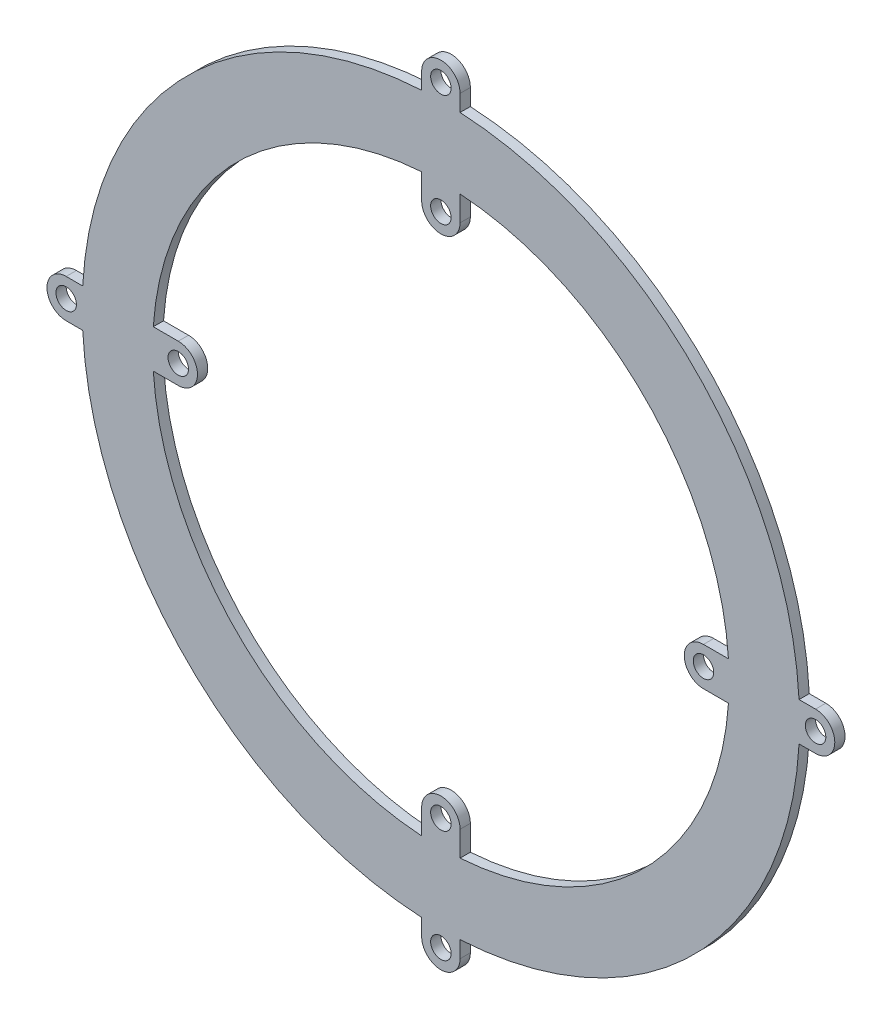
SolidWorks part; units mm, degrees
ref_plane "Front" through (0, 0, 0) normal (0, 0, 1) x (1, 0, 0)
ref_plane "Top" through (0, 0, 0) normal (0, 1, 0) x (1, 0, 0)
ref_plane "Right" through (0, 0, 0) normal (1, 0, 0) x (0, 0, -1)
sketch "Sketch1" plane through (0, 0, 0) normal (0, 0, 1) x (1, 0, 0)
  line L0 (58.5, 3) -> (55.9196, 3)
  line L1 (-3, 58.5) -> (-3, 55.9196)
  line L2 (3, 58.5) -> (3, 55.9196)
  line L3 (58.5, -3) -> (55.9196, -3)
  line L4 (3, -58.5) -> (3, -55.9196)
  line L5 (-3, -58.5) -> (-3, -55.9196)
  line L6 (-58.5, -3) -> (-55.9196, -3)
  line L7 (-58.5, 3) -> (-55.9196, 3)
  line L8 (41, 3) -> (44.8999, 3)
  line L9 (-3, 41) -> (-3, 44.8999)
  line L10 (3, 41) -> (3, 44.8999)
  line L11 (41, -3) -> (44.8999, -3)
  line L12 (3, -41) -> (3, -44.8999)
  line L13 (-3, -41) -> (-3, -44.8999)
  line L14 (-41, -3) -> (-44.8999, -3)
  line L15 (-41, 3) -> (-44.8999, 3)
  arc A0 (-3, 55.9196) -> (-55.9196, 3) centre (0, 0) ccw
  arc A1 (3, 58.5) -> (-3, 58.5) centre (0, 58.5) ccw
  circle A3 centre (0, 58.5) radius 1.6
  arc A4 (58.5, -3) -> (58.5, 3) centre (58.5, 0) ccw
  arc A5 (55.9196, 3) -> (3, 55.9196) centre (0, 0) ccw
  circle A6 centre (58.5, 0) radius 1.6
  arc A7 (-3, -58.5) -> (3, -58.5) centre (0, -58.5) ccw
  arc A8 (3, -55.9196) -> (55.9196, -3) centre (0, 0) ccw
  circle A9 centre (0, -58.5) radius 1.6
  arc A10 (-58.5, 3) -> (-58.5, -3) centre (-58.5, 0) ccw
  arc A11 (-55.9196, -3) -> (-3, -55.9196) centre (0, 0) ccw
  circle A12 centre (-58.5, 0) radius 1.6
  arc A13 (-55.9196, -3) -> (-3, -55.9196) centre (0, 0) ccw
  arc A14 (-55.9196, -3) -> (-3, -55.9196) centre (0, 0) ccw
  arc A15 (-55.9196, -3) -> (-3, -55.9196) centre (0, 0) ccw
  arc A16 (-3, 55.9196) -> (-55.9196, 3) centre (0, 0) ccw
  arc A17 (-3, 55.9196) -> (-55.9196, 3) centre (0, 0) ccw
  arc A18 (-3, 55.9196) -> (-55.9196, 3) centre (0, 0) ccw
  arc A19 (55.9196, 3) -> (3, 55.9196) centre (0, 0) ccw
  arc A20 (55.9196, 3) -> (3, 55.9196) centre (0, 0) ccw
  arc A21 (55.9196, 3) -> (3, 55.9196) centre (0, 0) ccw
  arc A22 (3, -55.9196) -> (55.9196, -3) centre (0, 0) ccw
  arc A23 (3, -55.9196) -> (55.9196, -3) centre (0, 0) ccw
  arc A24 (3, -55.9196) -> (55.9196, -3) centre (0, 0) ccw
  arc A25 (-3, 44.8999) -> (-44.8999, 3) centre (0, 0) ccw
  arc A26 (-3, 41) -> (3, 41) centre (0, 41) ccw
  circle A27 centre (0, 41) radius 1.6
  arc A28 (41, 3) -> (41, -3) centre (41, 0) ccw
  circle A29 centre (41, 0) radius 1.6
  arc A30 (3, -41) -> (-3, -41) centre (0, -41) ccw
  circle A31 centre (0, -41) radius 1.6
  arc A32 (-41, -3) -> (-41, 3) centre (-41, 0) ccw
  circle A33 centre (-41, 0) radius 1.6
  arc A34 (-44.8999, -3) -> (-3, -44.8999) centre (0, 0) ccw
  arc A35 (3, -44.8999) -> (44.8999, -3) centre (0, 0) ccw
  arc A36 (44.8999, 3) -> (3, 44.8999) centre (0, 0) ccw
  dimension "D1" = 4
  dimension "D2" = 4
extrude "Boss-Extrude1" add sketch "Sketch1" along normal blind 1.6 contours L6 A11 L5 A7 L4 A8 L3 A4 L0 A5 L2 A1 L1 A0 L7 A10 A36 L8 A28 L11 A35 L12 A30 L13 A34 L14 A32 L15 A25 L9 A26 L10 A33 A31 A29 A27 A12 A3 A6 A9
